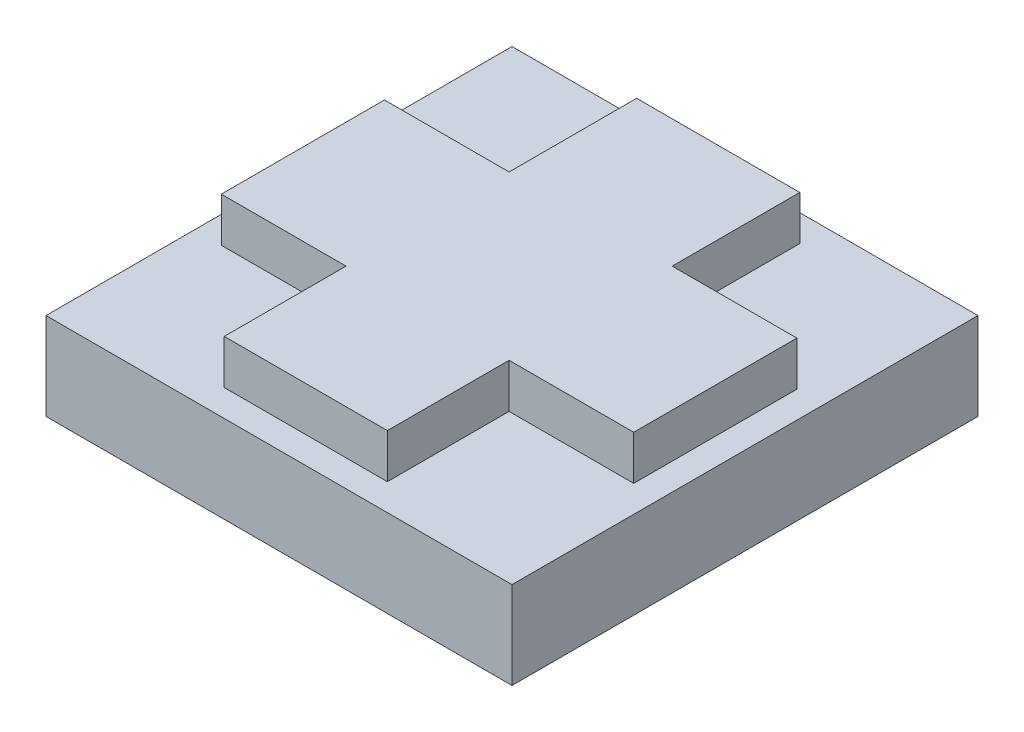
SolidWorks part; units mm, degrees
ref_plane "Front Plane" through (0, 0, 0) normal (0, 0, 1) x (1, 0, 0)
ref_plane "Top Plane" through (0, 0, 0) normal (0, 1, 0) x (1, 0, 0)
ref_plane "Right Plane" through (0, 0, 0) normal (1, 0, 0) x (0, 0, -1)
sketch "Sketch1" plane through (0, 0, 0) normal (0, 1, 0) x (1, 0, 0)
  line L1 (0, 0) -> (10.16, 0)
  line L2 (0, 0) -> (0, 10.16)
  line L3 (0, 10.16) -> (10.16, 10.16)
  line L4 (10.16, 0) -> (10.16, 10.16)
extrude "Boss-Extrude1" add sketch "Sketch1" along normal blind 1.905
sketch "Sketch2" plane through (0, 0, 0) normal (0, 1, 0) x (1, 0, 0)
  line L1 (3.302, 0.5842) -> (6.858, 0.5842)
  line L2 (3.302, 0.5842) -> (3.302, 9.5758)
  line L3 (3.302, 9.5758) -> (6.858, 9.5758)
  line L4 (6.858, 0.5842) -> (6.858, 9.5758)
extrude "Boss-Extrude4" add sketch "Sketch2" along normal blind 2.8702
sketch "Sketch4" plane through (0, 0, 0) normal (0, 1, 0) x (1, 0, 0)
  line L1 (0.5842, 6.7945) -> (9.5758, 6.7945)
  line L2 (0.5842, 6.7945) -> (0.5842, 3.2385)
  line L3 (0.5842, 3.2385) -> (9.5758, 3.2385)
  line L4 (9.5758, 6.7945) -> (9.5758, 3.2385)
extrude "Boss-Extrude5" add sketch "Sketch4" along normal blind 2.8702
sketch "Sketch5" plane through (0, 0, 0) normal (0, 1, 0) x (1, 0, 0)
  circle A0 centre (5.08, 5.08) radius 2.54
